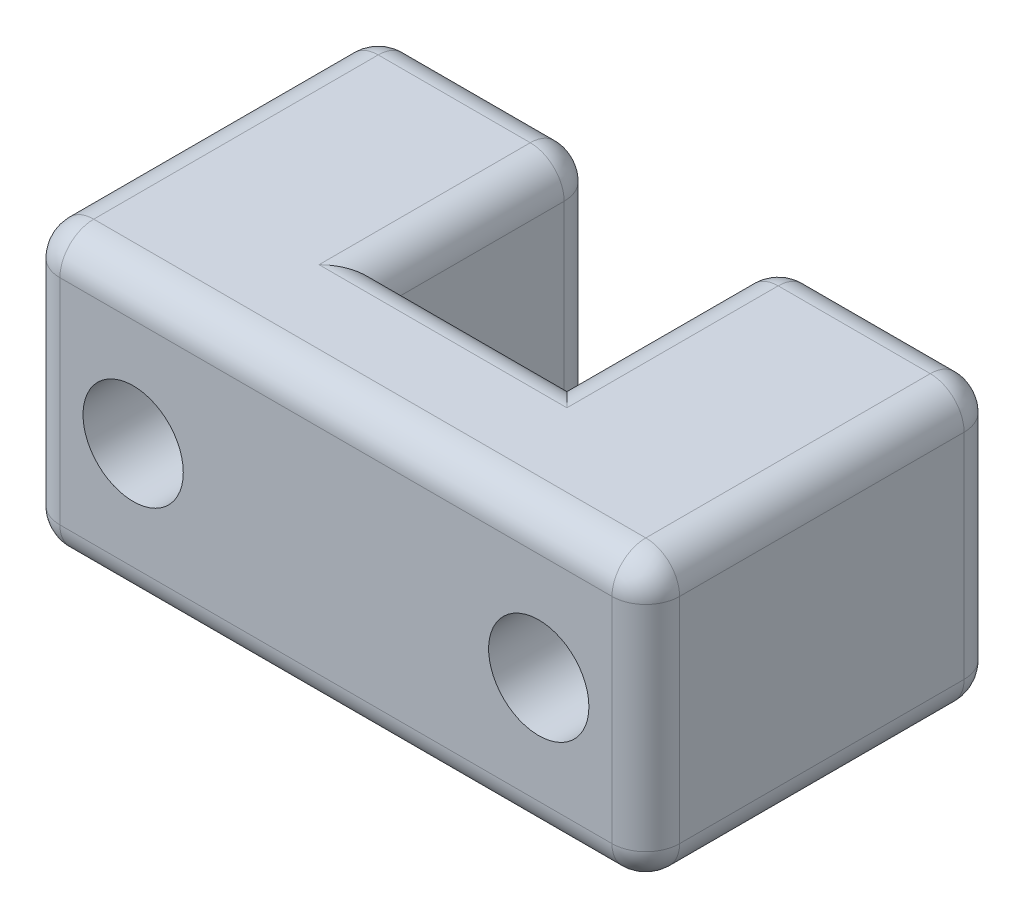
SolidWorks part; units mm, degrees
ref_plane "Front" through (0, 0, 0) normal (0, 0, 1) x (1, 0, 0)
ref_plane "Top" through (0, 0, 0) normal (0, 1, 0) x (1, 0, 0)
ref_plane "Right" through (0, 0, 0) normal (1, 0, 0) x (0, 0, -1)
sketch "Sketch1" plane through (0, 0, 0) normal (0, 1, 0) x (1, 0, 0)
  line L0 (0, 7.9375) -> (4.953, 7.9375)
  line L1 (0, 7.9375) -> (13.97, 7.9375) construction
  line L2 (0, 7.9375) -> (0, 0)
  line L3 (0, 0) -> (13.97, 0)
  line L4 (13.97, 7.9375) -> (13.97, 0)
  line L5 (4.953, 7.9375) -> (4.953, 3.175)
  line L6 (4.953, 3.175) -> (9.017, 3.175)
  line L7 (9.017, 3.175) -> (9.017, 7.9375)
  line L8 (9.017, 7.9375) -> (13.97, 7.9375)
  dimension "D1" = 13.97
  dimension "D2" = 4.064
  dimension "D3" = 4.7625
  dimension "D4" = 7.9375
extrude "Boss-Extrude1" add sketch "Sketch1" along normal blind 6.35
sketch "Sketch2" plane through (0, 0, 0) normal (0, 0, 1) x (1, 0, 0)
  line L0 (6.985, 6.35) -> (6.985, 0) construction
  line L1 (2.413, 3.175) -> (11.557, 3.175) construction
  line L2 (0, 6.35) -> (13.97, 6.35) construction
  line L3 (0, 0) -> (13.97, 0) construction
  circle A0 centre (2.413, 3.175) radius 1.1303
  circle A1 centre (11.557, 3.175) radius 1.1303
  point P8 (6.985, 3.175)
  dimension "D1" = 9.144
  dimension "D2" = 2.2606
extrude "Cut-Extrude1" cut sketch "Sketch2" against normal up to surface (7.9375 mm away) up to face at (11.4935, 3.175, -7.9375)
fillet "Fillet1" radius 0.762 22 edges at (2.4765, 6.35, -7.9375) (4.953, 6.35, -5.5563) (6.985, 6.35, -3.175) (9.017, 6.35, -5.5563) (11.4935, 6.35, -7.9375) (13.97, 6.35, -3.9688) (6.985, 6.35, 0) (0, 6.35, -3.9688) (6.985, 0, 0) (13.97, 0, -3.9688) (11.4935, 0, -7.9375) (9.017, 0, -5.5563) (6.985, 0, -3.175) (4.953, 0, -5.5563) (2.4765, 0, -7.9375) (0, 0, -3.9688) (0, 3.175, -7.9375) (0, 3.175, 0) (13.97, 3.175, 0) (13.97, 3.175, -7.9375) (4.953, 3.175, -7.9375) (9.017, 3.175, -7.9375)
